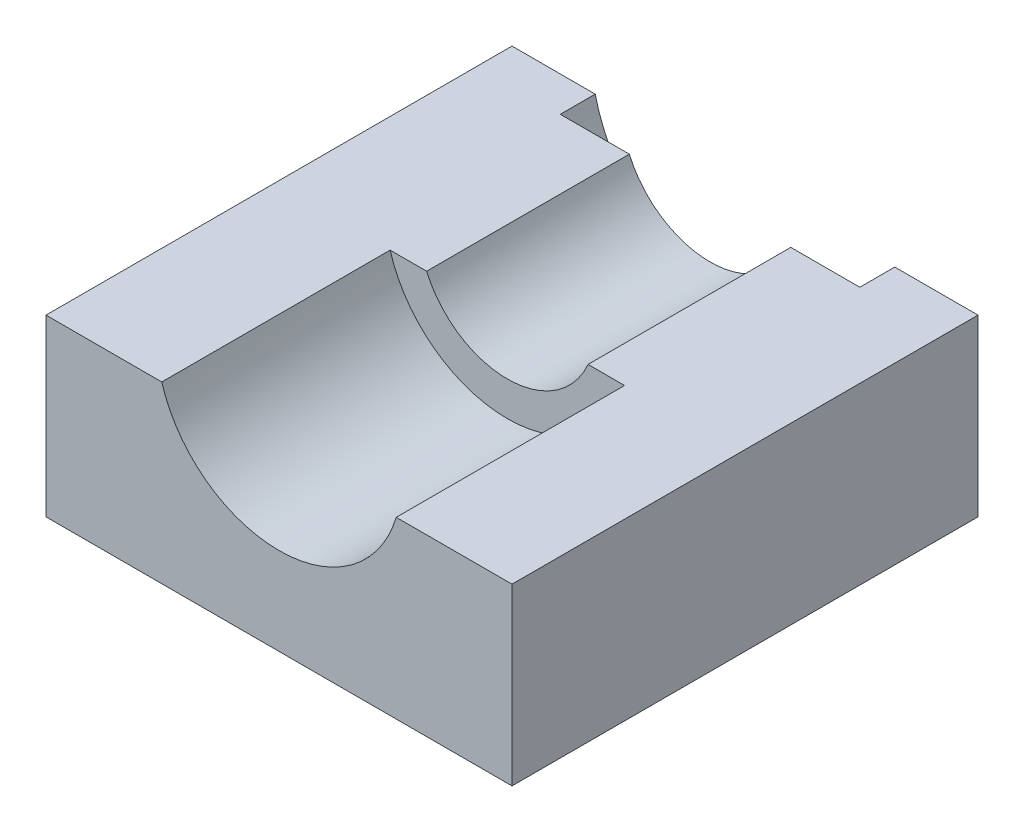
SolidWorks part; units mm, degrees
ref_plane "Front Plane" through (0, 0, 0) normal (0, 0, 1) x (1, 0, 0)
ref_plane "Top Plane" through (0, 0, 0) normal (0, 1, 0) x (1, 0, 0)
ref_plane "Right Plane" through (0, 0, 0) normal (1, 0, 0) x (0, 0, -1)
sketch "Sketch1" plane through (0, 0, 0) normal (0, 0, 1) x (1, 0, 0)
  line L1 (-100, -37.5) -> (100, -37.5)
  line L2 (-100, -37.5) -> (-100, 37.5)
  line L3 (-100, 37.5) -> (100, 37.5)
  line L4 (100, -37.5) -> (100, 37.5)
  line L5 (-100, -37.5) -> (100, 37.5) construction
  line L6 (-100, 37.5) -> (100, -37.5) construction
  point P0 (0, 0)
  dimension "D1" = 200
  dimension "D2" = 75
extrude "Boss-Extrude1" add sketch "Sketch1" along normal blind 200
sketch "Sketch2" plane through (0, 0, 200) normal (0, 0, 1) x (1, 0, 0)
  circle A0 centre (-0.0007, 52.4993) radius 52.5
extrude "Cut-Extrude1" cut sketch "Sketch2" against normal up to surface (98 mm away)
sketch "Sketch3" plane through (0, 0, 102) normal (0, 0, 1) x (1, 0, 0)
  circle A2 centre (-0.0007, 52.4993) radius 37.75
extrude "Cut-Extrude2" cut sketch "Sketch3" against normal up to surface (87 mm away)
sketch "Sketch4" plane through (0, 0, 15) normal (0, 0, 1) x (1, 0, 0)
  circle A0 centre (-0.0007, 52.4993) radius 66
extrude "Cut-Extrude3" cut sketch "Sketch4" against normal blind 200
